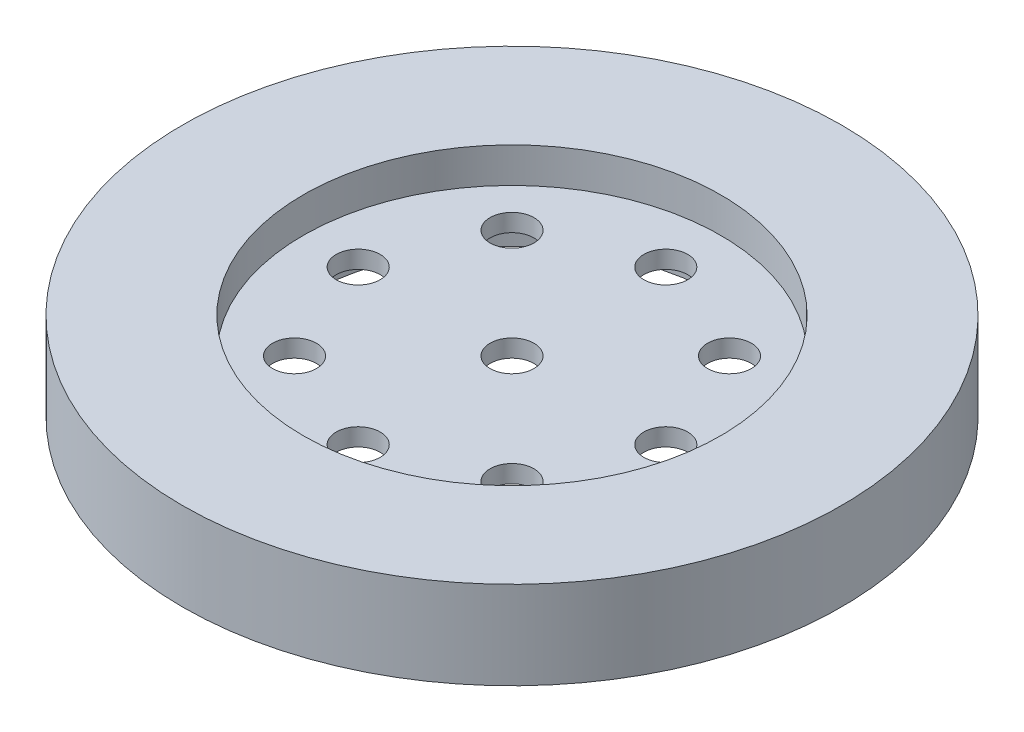
SolidWorks part; units mm, degrees
ref_plane "Front Plane" through (0, 0, 0) normal (0, 0, 1) x (1, 0, 0)
ref_plane "Top Plane" through (0, 0, 0) normal (0, 1, 0) x (1, 0, 0)
ref_plane "Right Plane" through (0, 0, 0) normal (1, 0, 0) x (0, 0, -1)
sketch "Sketch1" plane through (0, 0, 0) normal (0, 1, 0) x (1, 0, 0)
  circle A0 centre (0, 0) radius 43
  circle A1 centre (0, 0) radius 75
  dimension "D1" = 150
  dimension "D2" = 86
extrude "Boss-Extrude1" add sketch "Sketch1" along normal blind 20
sketch "Sketch2" plane through (0, 20, 0) normal (0, 1, 0) x (1, 0, 0)
  circle A0 centre (0, 0) radius 43
extrude "Boss-Extrude2" add sketch "Sketch2" against normal up to surface (20 mm away) up to face at (0, 0, 75)
sketch "Sketch3" plane through (0, 20, 0) normal (0, 1, 0) x (1, 0, 0)
  circle A0 centre (0, 0) radius 47.5
  dimension "D1" = 95
extrude "Cut-Extrude1" cut sketch "Sketch3" against normal blind 8
sketch "Sketch4" plane through (0, 0, 0) normal (0, -1, 0) x (1, 0, 0)
  circle A0 centre (0, 0) radius 47.5
  dimension "D1" = 95
sketch "Sketch6" plane through (0, 12, 0) normal (0, 1, 0) x (1, 0, 0)
  circle A0 centre (0, 0) radius 5
extrude "Cut-Extrude4" cut sketch "Sketch6" against normal through all
extrude "Cut-Extrude2" cut sketch "Sketch4" against normal blind 8
sketch "Sketch5" plane through (0, 12, 0) normal (0, 1, 0) x (1, 0, 0)
  circle A0 centre (0, 0) radius 3
  circle A1 centre (0, 0) radius 35 construction
  circle A2 centre (0, 35) radius 5
  circle A3 centre (24.7487, 24.7487) radius 5
  circle A4 centre (35, 0) radius 5
  circle A5 centre (24.7487, -24.7487) radius 5
  circle A6 centre (0, -35) radius 5
  circle A7 centre (-24.7487, -24.7487) radius 5
  circle A8 centre (-35, 0) radius 5
  circle A9 centre (-24.7487, 24.7487) radius 5
  point P22 (0, 0)
  dimension "D1" = 6
  dimension "D2" = 70
  dimension "D3" = 10
  dimension "D4" = 8
extrude "Cut-Extrude3" cut sketch "Sketch5" against normal through all
